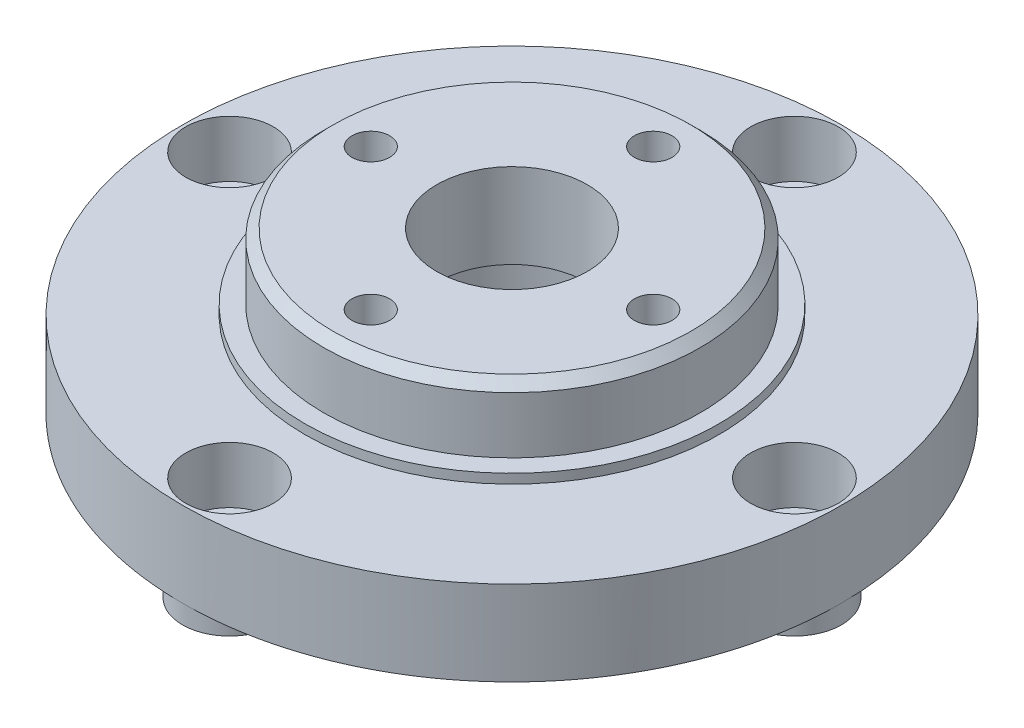
SolidWorks part; units mm, degrees
ref_plane "Front Plane" through (0, 0, 0) normal (0, 0, 1) x (1, 0, 0)
ref_plane "Top Plane" through (0, 0, 0) normal (0, 1, 0) x (1, 0, 0)
ref_plane "Right Plane" through (0, 0, 0) normal (1, 0, 0) x (0, 0, -1)
sketch "Sketch1" plane through (0, 0, 0) normal (0, 1, 0) x (1, 0, 0)
  circle A0 centre (0, 0) radius 11.1
  circle A1 centre (0, 0) radius 35
  circle A2 centre (0, 30) radius 2.65
  circle A3 centre (30, 0) radius 2.65
  circle A4 centre (0, -30) radius 2.65
  circle A5 centre (-30, 0) radius 2.65
  point P15 (0, 0)
  dimension "D1" = 22.2
  dimension "D2" = 70
  dimension "D4" = 5.3
  dimension "D3" = 30
  dimension "D5" = 4
extrude "Boss-Extrude1" add sketch "Sketch1" along normal blind 3
sketch "Sketch2" plane through (0, 3, 0) normal (0, 1, 0) x (1, 0, 0)
  circle A0 centre (0, 0) radius 35 construction
  circle A1 centre (0, 0) radius 11.1
  circle A3 centre (0, 0) radius 11.1
  circle A4 centre (0, 30) radius 2.65
  circle A5 centre (0, 30) radius 2.65
  circle A6 centre (30, 0) radius 2.65
  circle A7 centre (30, 0) radius 2.65
  circle A8 centre (0, -30) radius 2.65
  circle A9 centre (0, -30) radius 2.65
  circle A10 centre (-30, 0) radius 2.65
  circle A11 centre (-30, 0) radius 2.65
  circle A12 centre (0, 0) radius 35
  circle A13 centre (-30, 0) radius 4.65
  circle A14 centre (0, 30) radius 4.65
  circle A15 centre (30, 0) radius 4.65
  circle A16 centre (0, -30) radius 4.65
  circle M8 centre (0, 0) radius 35
  circle M9 centre (0, 0) radius 11.1
  dimension "D1" = 0
  dimension "D2" = 0
  dimension "D3" = 0
  dimension "D4" = 0
  dimension "D5" = 0
  dimension "D6" = 2
extrude "Boss-Extrude2" add sketch "Sketch2" along normal blind 6 contours A16 A15 A14 A13 M8 M9
sketch "Sketch3" plane through (0, 9, 0) normal (0, 1, 0) x (1, 0, 0)
  circle A0 centre (0, 0) radius 11.1 construction
  circle A1 centre (0, 0) radius 11.1
  circle A2 centre (0, 0) radius 8
  dimension "D1" = 16
extrude "Boss-Extrude3" add sketch "Sketch3" against normal blind 1
sketch "Sketch4" plane through (0, 9, 0) normal (0, 1, 0) x (1, 0, 0)
  circle A0 centre (0, 0) radius 20
  circle A1 centre (0, 0) radius 8 construction
  circle A2 centre (0, 0) radius 8
  dimension "D1" = 40
extrude "Boss-Extrude4" add sketch "Sketch4" along normal blind 8
sketch "Sketch5" plane through (0, 9, 0) normal (0, 1, 0) x (1, 0, 0)
  circle A0 centre (0, 0) radius 20 construction
  circle A1 centre (0, 0) radius 20
  circle A2 centre (0, 0) radius 22
  dimension "D1" = 2
extrude "Boss-Extrude5" add sketch "Sketch5" along normal blind 1
sketch "Sketch6" plane through (0, 0, 0) normal (0, -1, 0) x (-1, 0, 0)
  circle A0 centre (30, 0) radius 5
  circle A1 centre (0, 0) radius 35 construction
  circle A2 centre (30, 0) radius 2.65
  circle A3 centre (0, -30) radius 2.65
  circle A4 centre (0, -30) radius 5
  circle A5 centre (-30, 0) radius 2.65
  circle A6 centre (-30, 0) radius 5
  circle A7 centre (0, 30) radius 2.65
  circle A8 centre (0, 30) radius 5
  point P18 (0, 0)
  dimension "D1" = 5.3
  dimension "D2" = 4
extrude "Boss-Extrude6" add sketch "Sketch6" along normal blind 2
sketch "Sketch7" plane through (0, 17, 0) normal (0, 1, 0) x (1, 0, 0)
  circle A0 centre (0, 15) radius 2
  circle A1 centre (15, 0) radius 2
  circle A2 centre (0, -15) radius 2
  circle A3 centre (-15, 0) radius 2
  point P12 (0, 0)
  dimension "D2" = 4
  dimension "D1" = 15
  dimension "D3" = 4
extrude "Cut-Extrude1" cut sketch "Sketch7" against normal through all
chamfer "Chamfer1" distance 1 angle 45 2 edges at (0, 17, 20) (0, 0, 11.1)
